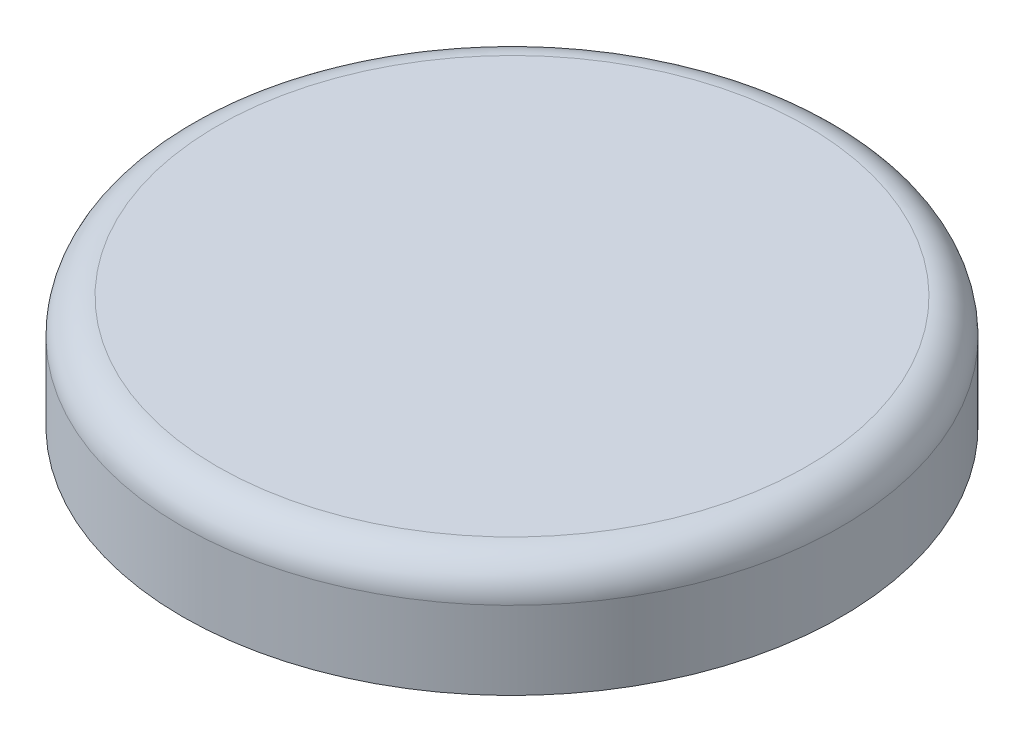
SolidWorks part; units mm, degrees
ref_plane "Front Plane" through (0, 0, 0) normal (0, 0, 1) x (1, 0, 0)
ref_plane "Top Plane" through (0, 0, 0) normal (0, 1, 0) x (1, 0, 0)
ref_plane "Right Plane" through (0, 0, 0) normal (1, 0, 0) x (0, 0, -1)
sketch "Sketch1" plane through (0, 0, 0) normal (0, 1, 0) x (1, 0, 0)
  circle A0 centre (0, 0) radius 7.6
  dimension "D1" = 15.2
extrude "Boss-Extrude1" add sketch "Sketch1" along normal blind 2.6
fillet "Fillet1" radius 0.8 1 edges at (0, 2.6, 7.6)
